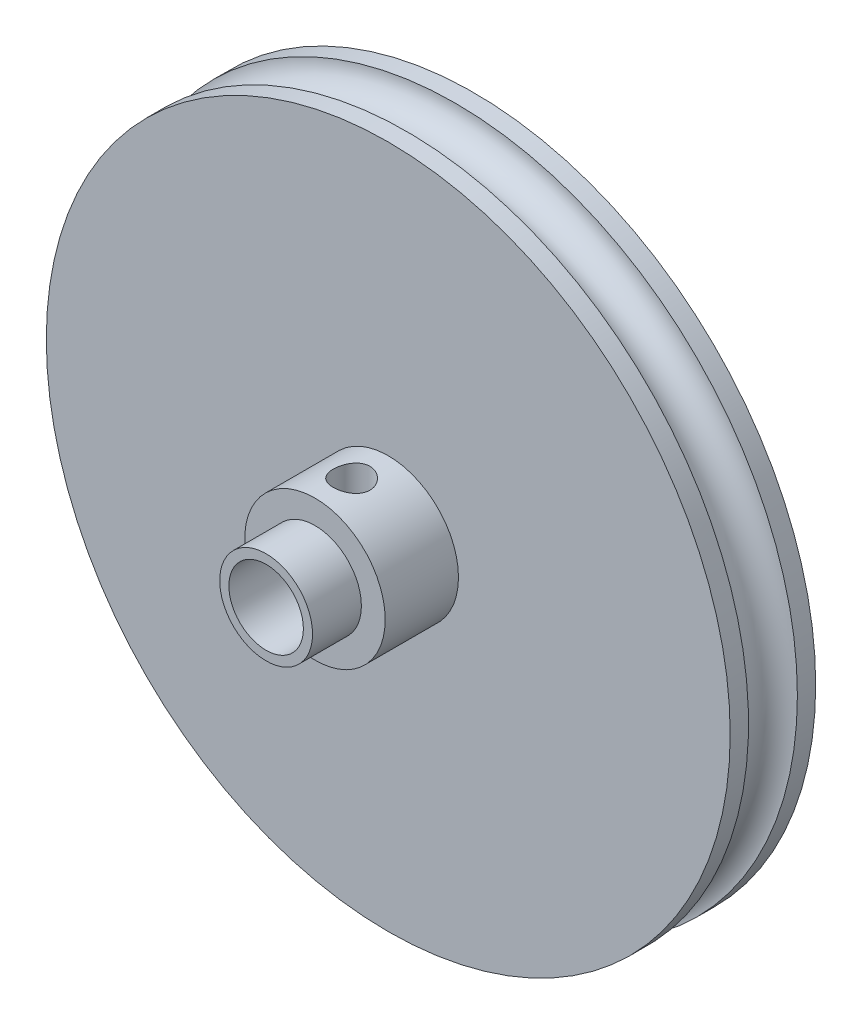
SolidWorks part; units mm, degrees
ref_plane "Plan de face" through (0, 0, 0) normal (0, 0, 1) x (1, 0, 0)
ref_plane "Plan de dessus" through (0, 0, 0) normal (0, 1, 0) x (1, 0, 0)
ref_plane "Plan de droite" through (0, 0, 0) normal (1, 0, 0) x (0, 0, -1)
sketch "Esquisse1" plane through (0, 0, 0) normal (0, 0, 1) x (1, 0, 0)
  circle A0 centre (0, 0) radius 28
  dimension "D1" = 56
extrude "Boss.-Extru.1" add sketch "Esquisse1" along normal blind 7
sketch "Esquisse2" plane through (0, 0, 7) normal (0, 0, 1) x (1, 0, 0)
  circle A0 centre (0, 0) radius 3.8
  dimension "D1" = 7.6
extrude "Boss.-Extru.2" add sketch "Esquisse2" along normal blind 10
sketch "Esquisse3" plane through (0, 0, 17) normal (0, 0, 1) x (1, 0, 0)
  circle A0 centre (0, 0) radius 3.05
  dimension "D1" = 6.1
extrude "Enlèv. mat.-Extru.1" cut sketch "Esquisse3" against normal through all
sketch "Esquisse4" plane through (0, 0, 0) normal (1, 0, 0) x (0, 0, -1)
  line L0 (-3.5, 28) -> (-3.5, 8.0945) construction
  line L1 (0, 28) -> (-7, 28) construction
  line L2 (0, 0) -> (-21.8888, 0) construction
  line L3 (-3.5, 0) -> (-3.5, -28) construction
  circle A1 centre (-3.5, 28) radius 2
  circle A2 centre (-3.5, -28) radius 2 construction
  dimension "D1" = 4
revolve "Enlèvement de matière-Révolution1" cut sketch "Esquisse4" angle 360 about L2
sketch "Esquisse5" plane through (0, 0, 7) normal (0, 0, 1) x (1, 0, 0)
  circle A0 centre (0, 0) radius 3.8
  circle A1 centre (0, 0) radius 5.75
  dimension "D1" = 11.5
  dimension "D2" = 7.6
extrude "Boss.-Extru.3" add sketch "Esquisse5" along normal blind 6
sketch "Esquisse6" plane through (0, 0, 0) normal (0, 1, 0) x (1, 0, 0)
  line L0 (0, -13) -> (0, -7) construction
  line L1 (-3.8, -13) -> (3.8, -13) construction
  line L2 (-5.75, -7) -> (5.75, -7) construction
  circle A0 centre (0, -10) radius 1.5
extrude "Enlèv. mat.-Extru.2" cut sketch "Esquisse6" along normal up to next
